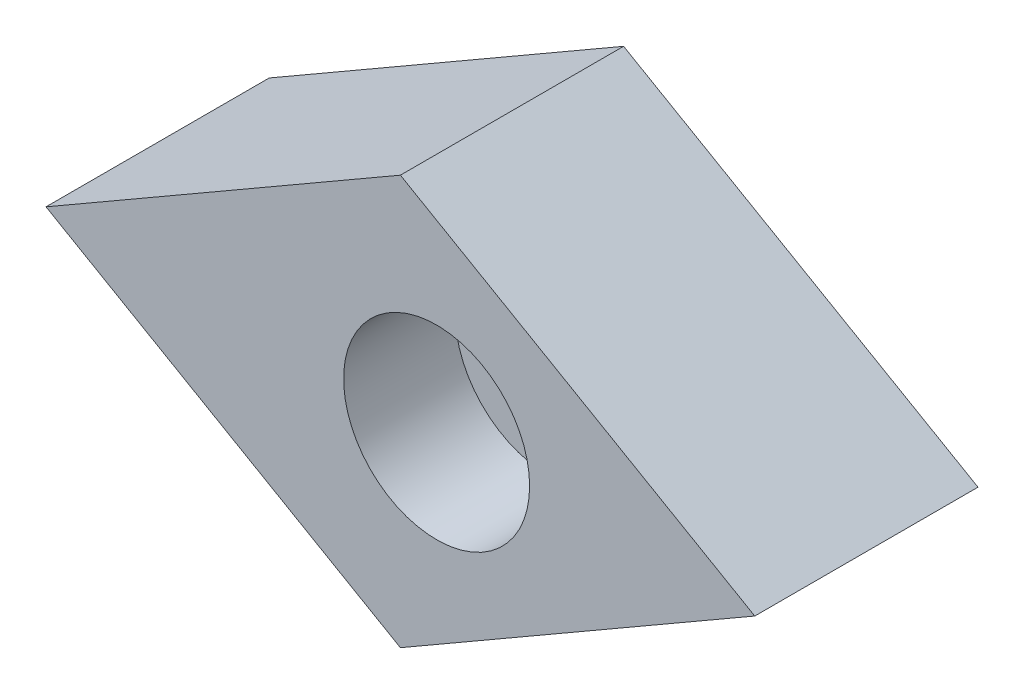
SolidWorks part; units mm, degrees
ref_plane "前视基准面" through (0, 0, 0) normal (0, 0, 1) x (1, 0, 0)
ref_plane "上视基准面" through (0, 0, 0) normal (0, 1, 0) x (1, 0, 0)
ref_plane "右视基准面" through (0, 0, 0) normal (1, 0, 0) x (0, 0, -1)
sketch "草图1" plane through (0, 0, 0) normal (0, 0, 1) x (1, 0, 0)
  line L0 (-44.476, 0) -> (34.3755, 0) construction
  line L1 (0, 42.0305) -> (0, -41.2691) construction
  line L2 (0, 5.5) -> (-9.5263, 0)
  line L3 (-9.5263, 0) -> (0, -5.5)
  line L4 (0, -5.5) -> (9.5263, 0)
  line L5 (9.5263, 0) -> (0, 5.5)
  dimension "D1" = 30
  dimension "D2" = 60
  dimension "D3" = 11
extrude "凸台-拉伸1" add sketch "草图1" along normal blind 6
sketch "草图2" plane through (0, 0, 6) normal (0, 0, 1) x (1, 0, 0)
  line L0 (-9.5263, 0) -> (9.5263, 0) construction
hole_wizard "孔1" positions "3D草图1" profile "草图3" legacy
sketch3d "3D草图1"
  line L0 (-9.5263, 0, 6) -> (9.5263, 0, 6) construction
  point P0 (0.9737, 0, 6)
  dimension "D1" = 10.5
sketch "草图3" plane through (0.9737, 0, 6) normal (1, 0, 0) x (0, -1, 0)
  line L0 (0, 0) -> (0, 6)
  line L1 (0, 6) -> (1.5, 6)
  line L2 (1.5, 6) -> (1.5, 3)
  line L3 (1.5, 3) -> (2.5, 3)
  line L4 (2.5, 3) -> (2.5, 0)
  line L5 (2.5, 0) -> (0, 0)
  line L6 (0, 110) -> (0, -10) construction
  dimension "直径" = 3
  dimension "深度" = 6
  dimension "柱坑直径" = 5
  dimension "柱坑深度" = 3
cosmetic thread "装饰螺纹线1" parameters "D2"=9
